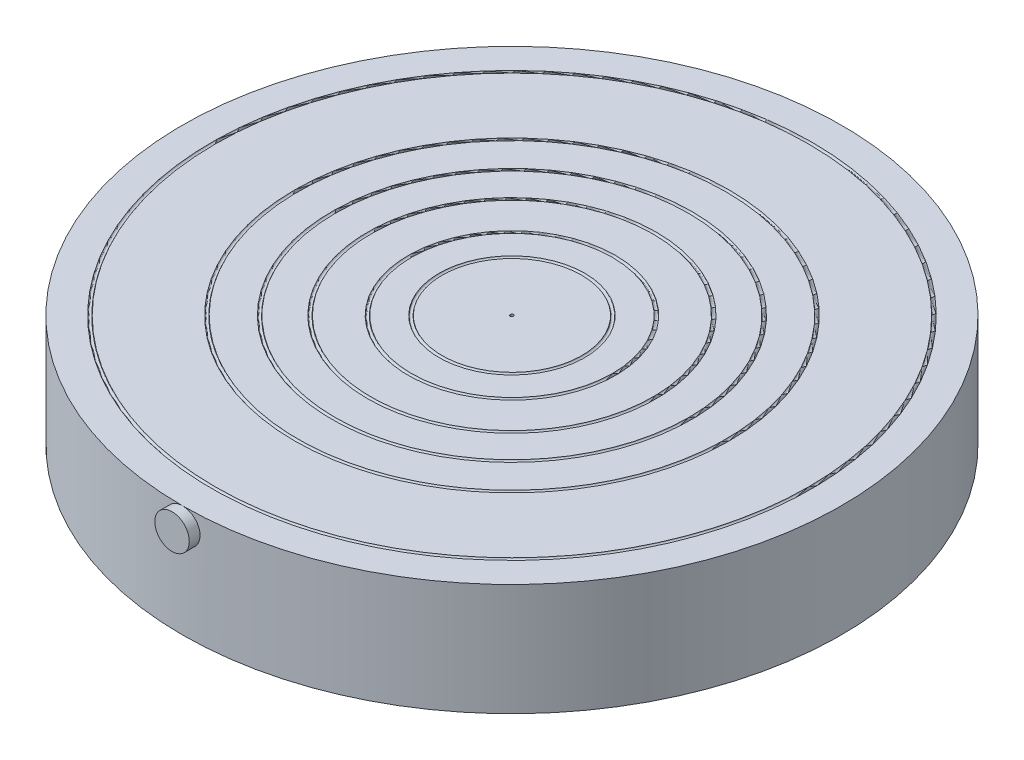
SolidWorks part; units mm, degrees
ref_plane "Front" through (0, 0, 0) normal (0, 0, 1) x (1, 0, 0)
ref_plane "Top" through (0, 0, 0) normal (0, 1, 0) x (1, 0, 0)
ref_plane "Right" through (0, 0, 0) normal (1, 0, 0) x (0, 0, -1)
sketch "Sketch1" plane through (0, 0, 0) normal (0, 1, 0) x (1, 0, 0)
  circle A0 centre (0, 0) radius 101.6
  dimension "D1" = 203.2
extrude "Extrude1" add sketch "Sketch1" along normal blind 34.5
sketch "Sketch3" plane through (0, 0, 0) normal (0, 0, 1) x (1, 0, 0)
  line L0 (0, 0) -> (0, 69) construction
  line L1 (101.6, 34.5) -> (-101.6, 34.5) construction
  line L2 (0, 34.5) -> (21.5, 34.5)
  line L3 (0, 34.5) -> (0, 39.5)
  line L4 (0, 39.5) -> (101.6, 39.5)
  line L5 (101.6, 34.5) -> (101.6, 39.5)
  line L6 (101.6, 0) -> (101.6, 34.5) construction
  line L7 (22, 34.5) -> (22, 42.4214) construction
  line L8 (31.5, 34.5) -> (31.5, 47.2497) construction
  line L9 (44, 34.5) -> (44, 47.2497) construction
  line L10 (55, 34.5) -> (55, 50.5035) construction
  line L11 (66.5, 34.5) -> (66.5, 49.139) construction
  line L12 (92, 34.5) -> (92, 64.1486) construction
  line L13 (92.5, 34.5) -> (101.6, 34.5)
  line L14 (91.5, 34.5) -> (92, 34.5) construction
  line L15 (92, 34.5) -> (92.5, 34.5) construction
  line L16 (67, 34.5) -> (91.5, 34.5)
  line L17 (55.5, 34.5) -> (66, 34.5)
  line L18 (44.5, 34.5) -> (54.5, 34.5)
  line L19 (32, 34.5) -> (43.5, 34.5)
  line L20 (22.5, 34.5) -> (31, 34.5)
  arc A0 (21.5, 34.5) -> (22.5, 34.5) centre (22, 34.5) ccw
  arc A1 (31, 34.5) -> (32, 34.5) centre (31.5, 34.5) ccw
  arc A2 (43.5, 34.5) -> (44.5, 34.5) centre (44, 34.5) ccw
  arc A3 (54.5, 34.5) -> (55.5, 34.5) centre (55, 34.5) ccw
  arc A4 (66, 34.5) -> (67, 34.5) centre (66.5, 34.5) ccw
  arc A5 (91.5, 34.5) -> (92.5, 34.5) centre (92, 34.5) ccw
  dimension "D8" = 1
  dimension "D1" = 5
  dimension "D2" = 92
  dimension "D3" = 66.5
  dimension "D4" = 55
  dimension "D5" = 44
  dimension "D6" = 31.5
  dimension "D7" = 22
revolve "Cut-Revolve1" cut sketch "Sketch3" angle 360 about L0
sketch "Sketch4" plane through (0, 34.5, 0) normal (0, 1, 0) x (1, 0, 0)
  circle A0 centre (0, 0) radius 0.5
  dimension "D1" = 1
extrude "Extrude2" cut sketch "Sketch4" against normal blind 1
ref_plane "Plane1" through (0, 0, 104.78) normal (0, 0, 1) x (1, 0, 0)
sketch "Sketch5" plane through (0, 0, 104.78) normal (0, 0, 1) x (1, 0, 0)
  line L0 (0, 0) -> (0, 189.4484) construction
  line L1 (21.5, 34.5) -> (-21.5, 34.5) construction
  circle A0 centre (0, 29.185) radius 5.315
  dimension "D1" = 10.63
extrude "Extrude3" add sketch "Sketch5" against normal up to body
